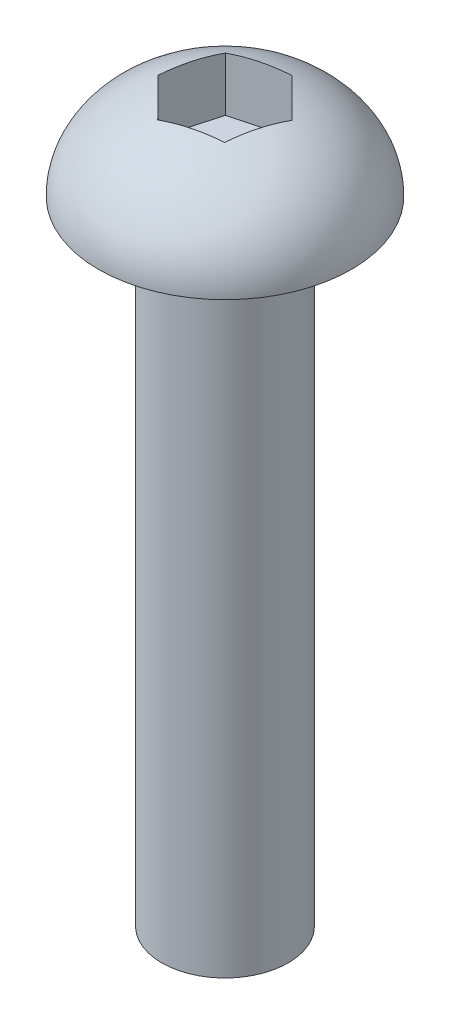
SolidWorks part; units mm, degrees
ref_plane "前视基准面" through (0, 0, 0) normal (0, 0, 1) x (1, 0, 0)
ref_plane "上视基准面" through (0, 0, 0) normal (0, 1, 0) x (1, 0, 0)
ref_plane "右视基准面" through (0, 0, 0) normal (1, 0, 0) x (0, 0, -1)
sketch "草图1" plane through (0, 0, 0) normal (0, 1, 0) x (1, 0, 0)
  circle A0 centre (0, 0) radius 1
  dimension "D1" = 2
extrude "凸台-拉伸1" add sketch "草图1" along normal blind 10
sketch "草图2" plane through (0, 10, 0) normal (0, 1, 0) x (1, 0, 0)
  circle A0 centre (0, 0) radius 2
  dimension "D1" = 4
extrude "凸台-拉伸2" add sketch "草图2" along normal blind 1.5
sketch "草图3" plane through (0, 11.5, 0) normal (0, 1, 0) x (1, 0, 0)
  line L1 (0.6093, -0.6154) -> (0.8376, 0.22)
  line L2 (0.8376, 0.22) -> (0.2283, 0.8354)
  line L3 (0.2283, 0.8354) -> (-0.6093, 0.6154)
  line L4 (-0.6093, 0.6154) -> (-0.8376, -0.22)
  line L5 (-0.8376, -0.22) -> (-0.2283, -0.8354)
  line L6 (-0.2283, -0.8354) -> (0.6093, -0.6154)
  circle A0 centre (0, 0) radius 0.75 construction
  dimension "D1" = 1.5
extrude "切除-拉伸1" cut sketch "草图3" against normal blind 1
sketch "草图5" plane through (0, 0, 0) normal (0, 0, 1) x (1, 0, 0)
  line L0 (-1, 10) -> (1, 10) construction
  line L1 (-2, 10) -> (2, 10) construction
  line L2 (-0.5, 11.5) -> (-2, 11.5)
  line L3 (-2, 10) -> (-2, 11.5)
  line L4 (-0.5, 11.5) -> (-0.5, 11.4524)
  line L5 (0, 11.5) -> (0, 10) construction
  ellipse E0 centre (0, 10) end of major axis (-2, 10) minor radius 1.5 (-0.5, 11.4524) -> (-2, 10) ccw
  point P17 (-0.5, 11.4762)
  dimension "D1" = 0.5
revolve "切除-旋转4" cut sketch "草图5" angle 360 about axis through (0, 11.5, 0) along (0, -1, 0)
